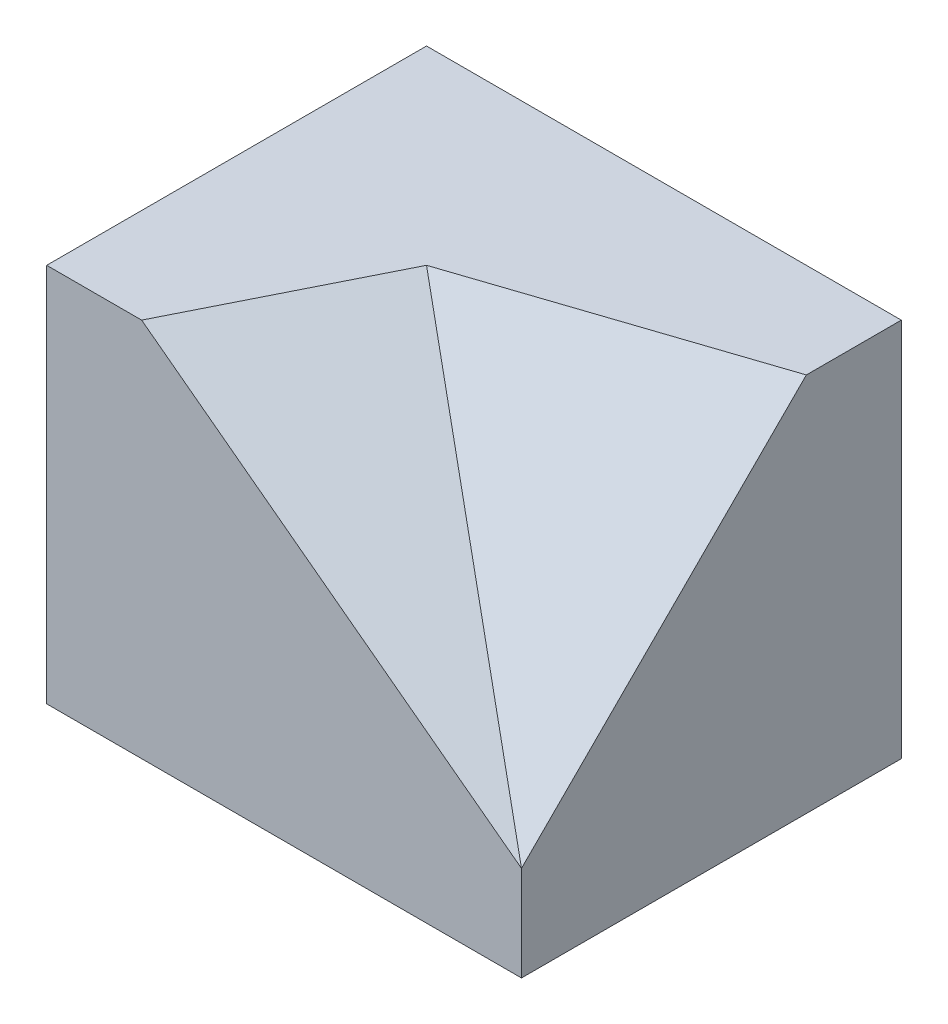
SolidWorks part; units mm, degrees
ref_plane "前基準面" through (0, 0, 0) normal (0, 0, 1) x (1, 0, 0)
ref_plane "上基準面" through (0, 0, 0) normal (0, 1, 0) x (1, 0, 0)
ref_plane "右基準面" through (0, 0, 0) normal (1, 0, 0) x (0, 0, -1)
sketch "草圖18" plane through (0, 0, 0) normal (0, 1, 0) x (1, 0, 0)
  line L1 (-25, -20) -> (25, -20)
  line L2 (-25, -20) -> (-25, 20)
  line L3 (-25, 20) -> (25, 20)
  line L4 (25, -20) -> (25, 20)
  line L5 (-25, -20) -> (25, 20) construction
  line L6 (-25, 20) -> (25, -20) construction
  point P0 (0, 0)
  dimension "D1" = 50
  dimension "D2" = 40
extrude "填料-伸長2" add sketch "草圖18" along normal blind 40
sketch "草圖25" plane through (0, 40, 0) normal (0, 1, 0) x (1, 0, 0)
  line L0 (25, -20) -> (-5, 0)
  line L1 (25, 20) -> (-25, 20) construction
  line L2 (-25, 20) -> (-25, -20) construction
  dimension "D1" = 20
  dimension "D2" = 20
ref_plane "平面4" through (-1.5385, 0, 2.3077) normal (0.5547, 0, -0.8321) x (-0.8321, 0, -0.5547)
sketch "草圖26" plane through (0, 0, 20) normal (0, 0, 1) x (1, 0, 0)
  line L0 (-15, 40) -> (25, 10)
  line L1 (-25, 40) -> (25, 40) construction
  line L2 (25, 40) -> (25, 0) construction
  line L3 (-25, 40) -> (-25, 0) construction
  dimension "D1" = 10
  dimension "D2" = 10
ref_plane "平面5" through (13.8, 18.4, 0) normal (-0.6, -0.8, 0) x (0.8, -0.6, 0)
sketch "草圖27" plane through (-1.5385, 0, 2.3077) normal (0.5547, 0, -0.8321) x (-0.8321, 0, -0.5547)
  line L0 (4.1603, 40) -> (-31.8953, 10)
ref_plane "平面6" through (15.9633, 21.2844, 7.9817) normal (0.5747, 0.7663, 0.2873) x (0.8184, -0.5381, -0.2018)
sketch "草圖28" plane through (15.9633, 21.2844, 7.9817) normal (0.5747, 0.7663, 0.2873) x (0.8184, -0.5381, -0.2018)
  line L0 (-37.8355, -4.6816) -> (-25.616, 14.0449)
  line L1 (-25.616, 14.0449) -> (11.0424, -15.2153)
  line L2 (11.0424, -15.2153) -> (-37.8355, -4.6816)
extrude "除料-伸長9" cut sketch "草圖28" along normal blind 40
sketch "草圖30" plane through (25, 0, 0) normal (1, 0, 0) x (0, 0, -1)
  line L0 (-20, 10) -> (10, 40)
  line L1 (-17.8571, 40) -> (20, 40) construction
  dimension "D1" = 10
ref_plane "平面7" through (6.0526, 18.1579, 18.1579) normal (-0.2294, -0.6882, -0.6882) x (-0.9733, 0.1622, 0.1622)
sketch "草圖31" plane through (6.0526, 18.1579, 18.1579) normal (-0.2294, -0.6882, -0.6882) x (-0.9733, 0.1622, 0.1622)
  line L0 (11.3555, 28.2843) -> (-19.4666, 35.3553)
  line L1 (-19.4666, 35.3553) -> (-19.4666, -7.0711)
  line L2 (-19.4666, -7.0711) -> (11.3555, 28.2843)
  line L3 (-19.4666, -7.0711) -> (11.3555, 28.2843) construction
  point P4 (11.7453, 28.7314)
extrude "除料-伸長10" cut sketch "草圖31" against normal blind 40
